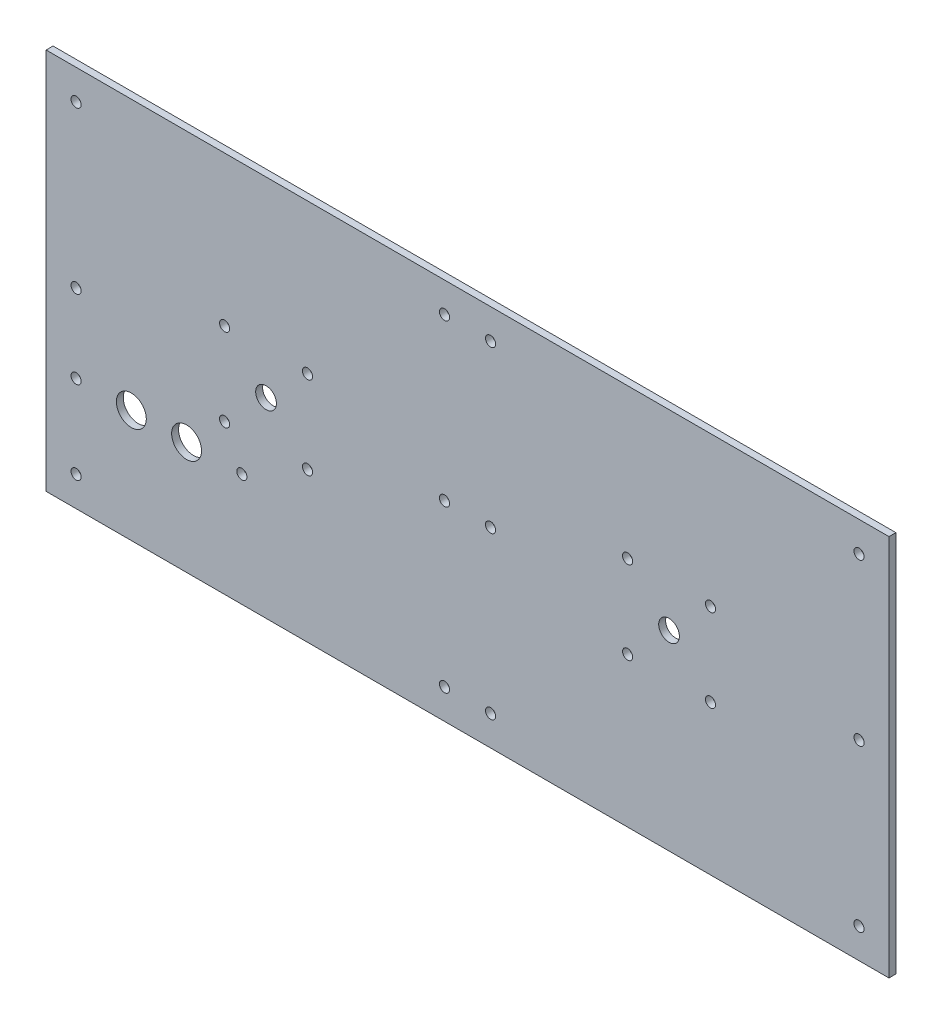
SolidWorks part; units mm, degrees
ref_plane "Plan de face" through (0, 0, 0) normal (0, 0, 1) x (1, 0, 0)
ref_plane "Plan de dessus" through (0, 0, 0) normal (0, 1, 0) x (1, 0, 0)
ref_plane "Plan de droite" through (0, 0, 0) normal (1, 0, 0) x (0, 0, -1)
sketch "Esquisse1" plane through (0, 0, 0) normal (0, 0, 1) x (1, 0, 0)
  line L0 (13, 166) -> (13, 0) construction
  line L1 (0, 0) -> (366, 0)
  line L2 (0, 0) -> (0, 166)
  line L3 (0, 166) -> (366, 166)
  line L4 (366, 0) -> (366, 166)
  line L5 (183, 166) -> (183, 83) construction
  line L6 (183, 83) -> (366, 83) construction
  line L7 (0, 153) -> (366, 153) construction
  line L8 (353, 166) -> (353, 0) construction
  line L9 (0, 13) -> (366, 13) construction
  line L10 (353, 166) -> (353, 0) construction
  line L11 (37, 49) -> (61, 49) construction
  line L12 (77.5, 101) -> (113.5, 101) construction
  line L13 (77.5, 101) -> (77.5, 65) construction
  line L14 (77.5, 65) -> (113.5, 65) construction
  line L15 (113.5, 101) -> (113.5, 65) construction
  line L16 (77.5, 101) -> (113.5, 65) construction
  line L17 (77.5, 65) -> (113.5, 101) construction
  circle A0 centre (13, 153) radius 2.2
  circle A1 centre (13, 13) radius 2.2
  circle A2 centre (13, 83) radius 2.2
  circle A3 centre (173, 153) radius 2.2
  circle A4 centre (193, 83) radius 2.2
  circle A5 centre (173, 83) radius 2.2
  circle A6 centre (193, 153) radius 2.2
  circle A7 centre (353, 83) radius 2.2
  circle A8 centre (353, 13) radius 2.2
  circle A9 centre (353, 153) radius 2.2
  circle A10 centre (193, 13) radius 2.2
  circle A11 centre (173, 13) radius 2.2
  circle A12 centre (270.5, 83) radius 4.5
  circle A13 centre (95.5, 83) radius 4.5
  circle A14 centre (77.5, 101) radius 2.2
  circle A15 centre (113.5, 101) radius 2.2
  circle A16 centre (77.5, 65) radius 2.2
  circle A17 centre (113.5, 65) radius 2.2
  circle A18 centre (288.5, 65) radius 2.2
  circle A19 centre (252.5, 65) radius 2.2
  circle A20 centre (252.5, 101) radius 2.2
  circle A21 centre (288.5, 101) radius 2.2
  circle A22 centre (37, 49) radius 6.5
  circle A23 centre (61, 49) radius 6.5
  circle A24 centre (85, 49) radius 2.2
  circle A25 centre (13, 49) radius 2.2
  point P68 (0, 0)
  dimension "D5" = 4.4
  dimension "D8" = 9
  dimension "D11" = 4.4
  dimension "D12" = 13
  dimension "D16" = 4.4
  dimension "D1" = 366
  dimension "D2" = 166
  dimension "D3" = 13
  dimension "D4" = 13
  dimension "D6" = 10
  dimension "D7" = 10
  dimension "D9" = 175
  dimension "D10" = 36
  dimension "D13" = 36
  dimension "D14" = 24
  dimension "D15" = 24
  dimension "D17" = 24
extrude "Boss.-Extru.1" add sketch "Esquisse1" along normal blind 3
